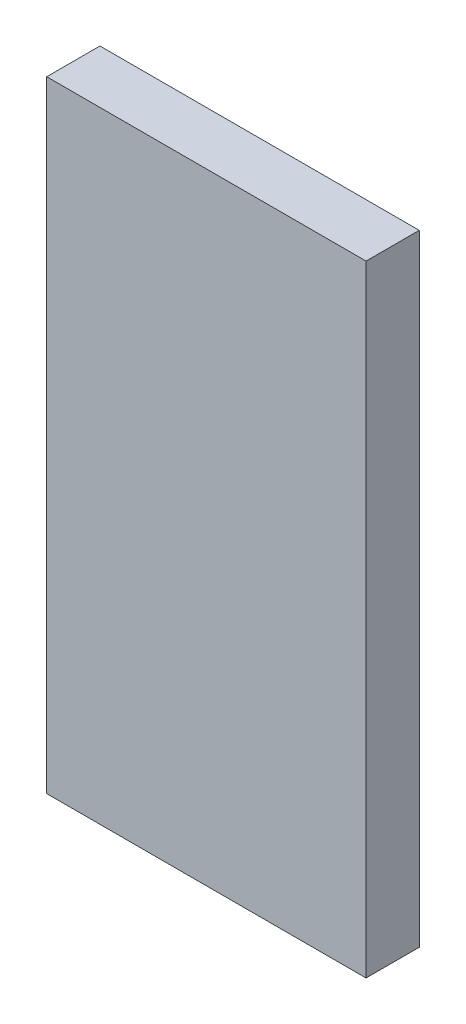
SolidWorks part; units mm, degrees
material "Silicon Rubber"
ref_plane "Front Plane" through (0, 0, 0) normal (0, 0, 1) x (1, 0, 0)
ref_plane "Top Plane" through (0, 0, 0) normal (0, 1, 0) x (1, 0, 0)
ref_plane "Right Plane" through (0, 0, 0) normal (1, 0, 0) x (0, 0, -1)
sketch "Sketch1" plane through (0, 0, 0) normal (0, 0, 1) x (1, 0, 0)
  line L0 (0, 35) -> (0, 0)
  line L1 (0, 35) -> (18, 35)
  line L2 (18, 35) -> (18, 0)
  line L3 (18, 0) -> (0, 0)
  dimension "D1" = 18
  dimension "D2" = 35
extrude "Boss-Extrude1" add sketch "Sketch1" along normal blind 3
